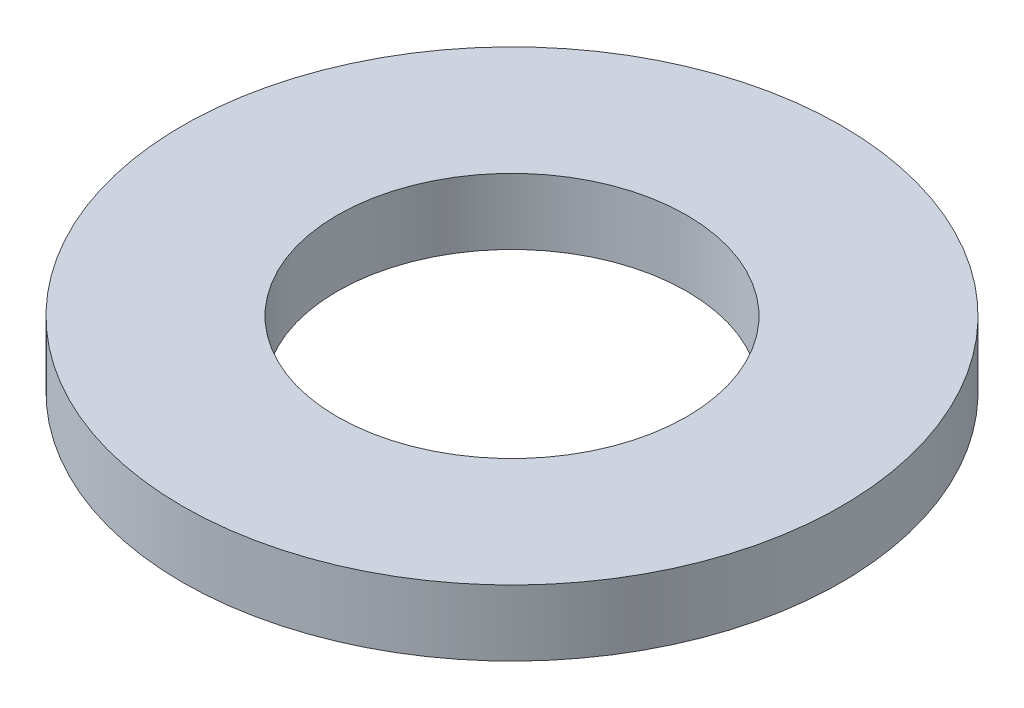
SolidWorks part; units mm, degrees
ref_plane "Front" through (0, 0, 0) normal (0, 0, 1) x (1, 0, 0)
ref_plane "Top" through (0, 0, 0) normal (0, 1, 0) x (1, 0, 0)
ref_plane "Right" through (0, 0, 0) normal (1, 0, 0) x (0, 0, -1)
sketch "Sketch1" plane through (0, 0, 0) normal (0, 1, 0) x (1, 0, 0)
  circle A0 centre (0, 0) radius 2.65
  circle A1 centre (0, 0) radius 5
  dimension "D1" = 5.3
  dimension "D2" = 10
extrude "Boss-Extrude1" add sketch "Sketch1" along normal blind 1
